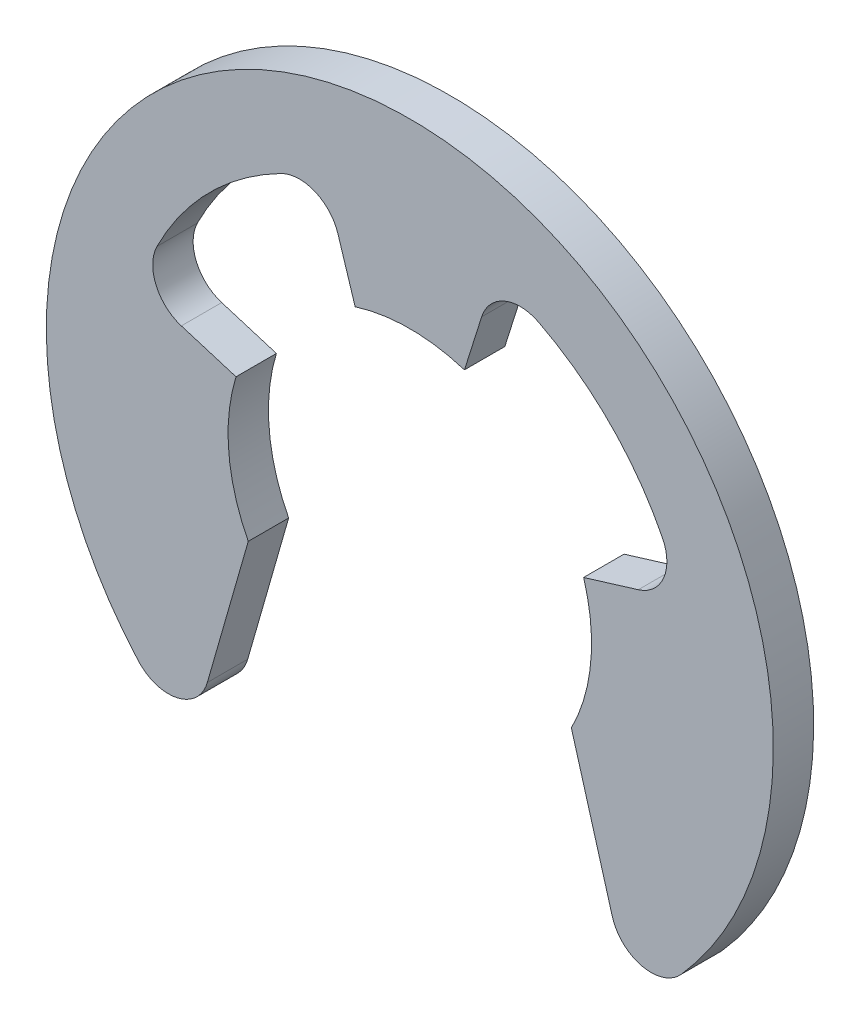
SolidWorks part; units mm, degrees
ref_plane "前视基准面" through (0, 0, 0) normal (0, 0, 1) x (1, 0, 0)
ref_plane "上视基准面" through (0, 0, 0) normal (0, 1, 0) x (1, 0, 0)
ref_plane "右视基准面" through (0, 0, 0) normal (1, 0, 0) x (0, 0, -1)
sketch "草图1" plane through (0, 0, 0) normal (0, 0, 1) x (1, 0, 0)
  line L0 (0, 0) -> (6.9734, 0.6101) construction
  line L1 (-2.193, 0) -> (1.9152, 0) construction
  line L2 (0, -1.8051) -> (0, 1.7867) construction
  line L3 (4, -2.0616) -> (5.0134, -5.5957)
  line L4 (-4, -2.0616) -> (-5.0134, -5.5957)
  line L5 (1.3532, 4.2917) -> (1.779, 5.6423)
  line L6 (-1.3532, 4.2917) -> (-1.779, 5.6423)
  line L7 (0, 0) -> (1.3532, 4.2917) construction
  line L8 (1.3532, 4.2917) -> (0, 0) construction
  line L9 (0, 0) -> (-1.3532, 4.2917) construction
  line L10 (4.3034, 1.3157) -> (5.6576, 1.7297)
  line L11 (-4.3034, 1.3157) -> (-5.6576, 1.7297)
  line L12 (0, 0) -> (4.3034, 1.3157) construction
  line L13 (4.3034, 1.3157) -> (0, 0) construction
  line L14 (0, 0) -> (-4.3034, 1.3157) construction
  arc A0 (4, -2.0616) -> (4.3034, 1.3157) centre (0, 0) ccw
  arc A1 (7, 0) -> (6.9734, 0.6101) centre (0, 0) ccw
  arc A2 (6.7215, -5.9851) -> (-6.7215, -5.9851) centre (0, 0) ccw
  arc A3 (-3.1882, 6.2318) -> (-6.2594, 3.1337) centre (0, 0) ccw
  arc A4 (-4.3034, 1.3157) -> (-4, -2.0616) centre (0, 0) ccw
  arc A5 (1.3532, 4.2917) -> (-1.3532, 4.2917) centre (0, 0) ccw
  arc A6 (6.2594, 3.1337) -> (3.1882, 6.2318) centre (0, 0) ccw
  arc A7 (-5.0134, -5.5957) -> (-6.7215, -5.9851) centre (-5.9747, -5.3201) cw
  arc A8 (6.7215, -5.9851) -> (5.0134, -5.5957) centre (5.9747, -5.3201) cw
  arc A9 (-6.2594, 3.1337) -> (-5.6576, 1.7297) centre (-5.3652, 2.686) ccw
  arc A10 (-1.779, 5.6423) -> (-3.1882, 6.2318) centre (-2.7327, 5.3416) ccw
  arc A11 (3.1882, 6.2318) -> (1.779, 5.6423) centre (2.7327, 5.3416) ccw
  arc A12 (6.2594, 3.1337) -> (5.6576, 1.7297) centre (5.3652, 2.686) cw
  point P22 (-5.4603, -7.1544)
  point P25 (5.4603, -7.1544)
  point P30 (-2.1049, 6.676)
  point P33 (2.1049, 6.676)
  point P36 (6.6941, 2.0466)
  dimension "D1" = 5
  dimension "d" = 9
  dimension "D3" = 17
  dimension "DD" = 18
  dimension "r" = 1
  dimension "D2" = 35
  dimension "RR" = 7
  dimension "D4" = 17
  dimension "angle" = 16
  dimension "B" = 8
extrude "拉伸1" add sketch "草图1" along normal blind 1
